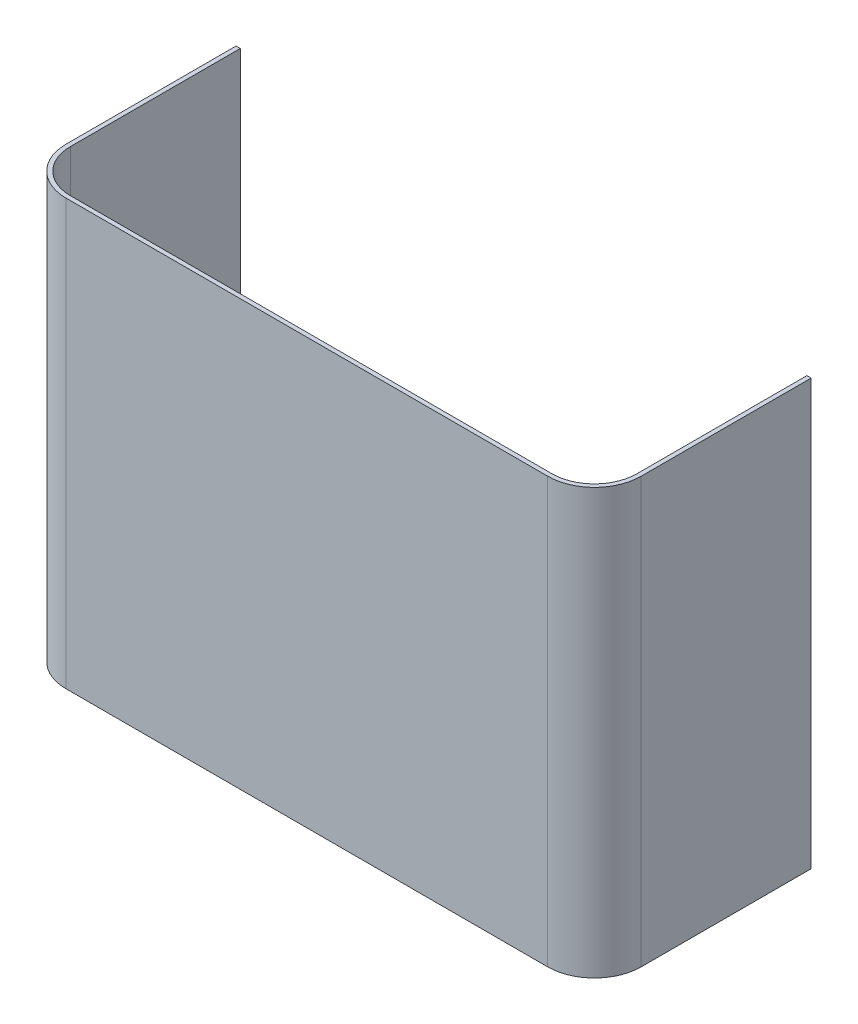
SolidWorks part; units mm, degrees
material "PPE"
ref_plane "Front Plane" through (0, 0, 0) normal (0, 0, 1) x (1, 0, 0)
ref_plane "Top Plane" through (0, 0, 0) normal (0, 1, 0) x (1, 0, 0)
ref_plane "Right Plane" through (0, 0, 0) normal (1, 0, 0) x (0, 0, -1)
sketch "Sketch1" plane through (0, 0, 0) normal (0, 1, 0) x (1, 0, 0)
  line L1 (-170, -75) -> (170, -75)
  line L2 (-200, -45) -> (-200, 75)
  line L3 (-200, 75) -> (200, 75)
  line L4 (200, -45) -> (200, 75)
  line L5 (-200, -75) -> (200, 75) construction
  line L6 (-200, 75) -> (200, -75) construction
  arc A0 (200, -45) -> (170, -75) centre (170, -45) cw
  arc A1 (-170, -75) -> (-200, -45) centre (-170, -45) cw
  point P0 (0, 0)
  dimension "D3" = 30
  dimension "D1" = 400
  dimension "D2" = 150
sketch "Sketch3" plane through (0, 0, 0) normal (1, 0, 0) x (0, 0, -1)
  line L0 (0, 0) -> (0, 300)
  line L1 (0, 0) -> (-127.1041, 0) construction
  dimension "D1" = 90
  dimension "D2" = 300
sweep "Sweep-Thin1" add profiles "Sketch1" path "Sketch3" parameters "D1"=3
sketch "Sketch4" plane through (0, 0, -78) normal (0, 0, -1) x (-1, 0, 0)
  line L1 (447.7687, -695.9593) -> (-275.2158, -695.9593)
  line L2 (447.7687, -695.9593) -> (447.7687, 381.8083)
  line L3 (447.7687, 381.8083) -> (-275.2158, 381.8083)
  line L4 (-275.2158, -695.9593) -> (-275.2158, 381.8083)
  line L5 (447.7687, -695.9593) -> (-275.2158, 381.8083) construction
  line L6 (447.7687, 381.8083) -> (-275.2158, -695.9593) construction
  point P0 (86.2765, -157.0755)
extrude "Cut-Extrude1" cut sketch "Sketch4" against normal blind 3
